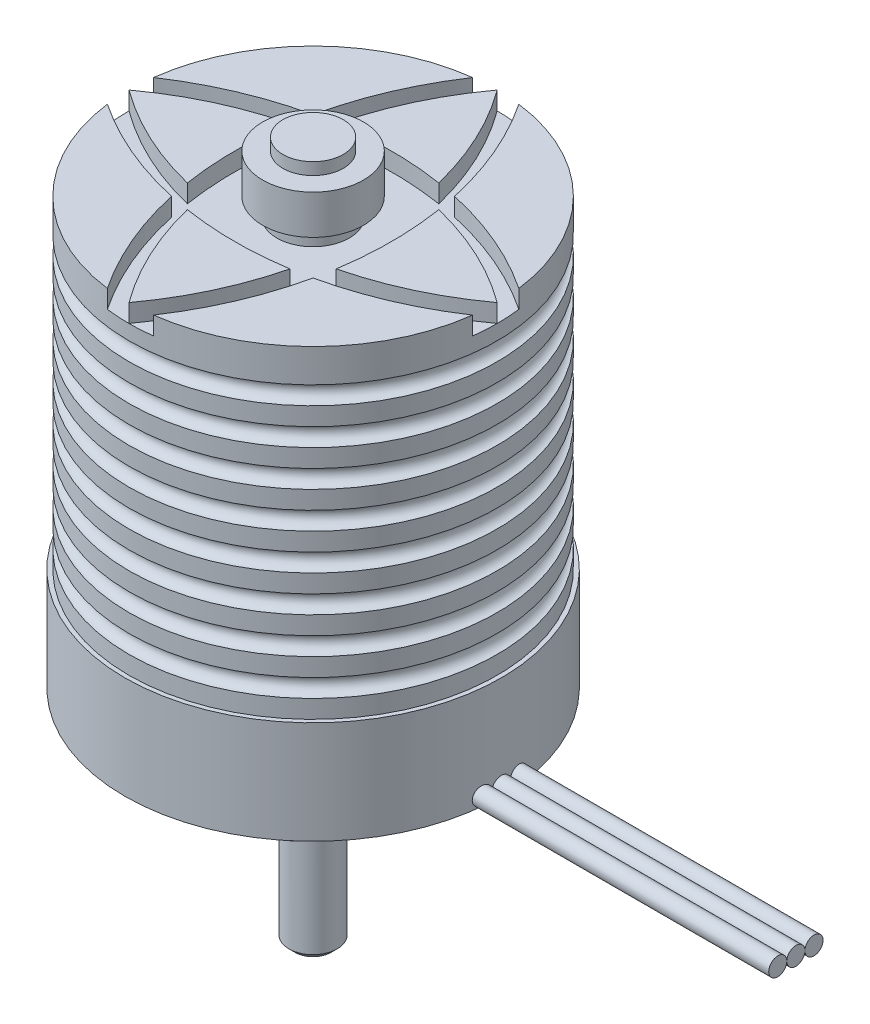
SolidWorks part; units mm, degrees
material "Plain Carbon Steel"
ref_plane "Front" through (0, 0, 0) normal (0, 0, 1) x (1, 0, 0)
ref_plane "Top" through (0, 0, 0) normal (0, 1, 0) x (1, 0, 0)
ref_plane "Right" through (0, 0, 0) normal (1, 0, 0) x (0, 0, -1)
sketch "Sketch1" plane through (0, 0, 0) normal (0, 1, 0) x (1, 0, 0)
  circle A0 centre (0, 0) radius 30.5
  dimension "D1" = 61
extrude "Boss-Extrude1" add sketch "Sketch1" along normal blind 53.5
sketch "Sketch3" plane through (0, 0, 0) normal (0, -1, 0) x (1, 0, 0)
  circle A2 centre (0, 0) radius 31.2
  dimension "D1" = 62.4
ref_plane "Plane1" through (0, -17, 0) normal (0, -1, 0) x (-1, 0, 0)
extrude "Boss-Extrude3" add sketch "Sketch3" along normal up to surface (17 mm away) separate body up to plane "Plane1"
sketch "Sketch2" plane through (0, 0, 0) normal (0, 1, 0) x (1, 0, 0)
  circle A0 centre (0, 0) radius 4
  dimension "D1" = 8
extrude "Boss-Extrude2" add sketch "Sketch2" against normal offset from surface (107 mm away) 36.5 from surface at 53.5 separate body up to face at (0, -17, -31.2) offset beyond the face yes starting at face at (0, 53.5, 30.5)
sketch "Sketch4" plane through (0, 0, 0) normal (0, 0, 1) x (1, 0, 0)
  line L1 (30.5, 0) -> (30.5, 53.5) construction
  line L2 (30.5, 0) -> (-30.5, 0)
  line L3 (30.5, 0) -> (30.5, 53.5)
  line L4 (30.5, 6) -> (30.5, 3)
  line L5 (0, 0) -> (0, 6.4095) construction
  arc A0 (30.5, 6) -> (30.5, 3) centre (30.5, 4.5) ccw
  dimension "D1" = 3
  dimension "D2" = 3
revolve "Cut-Revolve1" cut sketch "Sketch4" angle 360 about L5
pattern_linear "LPattern3" count 8 spacing 6 along (0, 1, 0) of "Cut-Revolve1"
hole_wizard "Tap Drill for M4x0.7 Tap1" positions "Sketch5" profile "Sketch6" hole size "M4x0.7" standard "ANSI Metric" end condition through all
sketch "Sketch5" plane through (0, -17, 0) normal (0, -1, 0) x (-1, 0, 0)
  line L1 (15.5563, 15.5563) -> (-15.5563, 15.5563) construction
  line L2 (15.5563, 15.5563) -> (15.5563, -15.5563) construction
  line L3 (15.5563, -15.5563) -> (-15.5563, -15.5563) construction
  line L4 (-15.5563, 15.5563) -> (-15.5563, -15.5563) construction
  line L5 (15.5563, 15.5563) -> (-15.5563, -15.5563) construction
  line L6 (15.5563, -15.5563) -> (-15.5563, 15.5563) construction
  point P2 (-15.5563, -15.5563)
  point P115 (15.5563, 15.5563)
  point P116 (15.5563, -15.5563)
  point P117 (-15.5563, 15.5563)
  dimension "D1" = 44
sketch "Sketch6" plane through (15.5563, -17, 15.5563) normal (1, 0, 0) x (0, 0, -1)
  line L0 (0, 0) -> (0, 17)
  line L1 (0, 17) -> (1.65, 17)
  line L2 (1.65, 17) -> (1.65, 0)
  line L5 (1.65, 0) -> (0, 0)
  line L11 (0, -6.35) -> (0, 107.95) construction
  dimension "Thru Hole Dia." = 3.3
  dimension "Thru Hole Depth" = 17
pattern_circular "CirPattern1" count 2 every 15 about axis through (0, 0, 0) along (0, 1, 0) of "Tap Drill for M4x0.7 Tap1"
sketch "Sketch7" plane through (0, -53.5, 0) normal (0, -1, 0) x (1, 0, 0)
  circle A1 centre (0, 0) radius 4
  circle A2 centre (0, 0) radius 4
  dimension "D1" = 0
extrude "Cut-Extrude1" cut sketch "Sketch7" against normal through all
sketch "Sketch8" plane through (0, 53.5, 0) normal (0, 1, 0) x (1, 0, 0)
  arc A0 (0, -30.5) -> (0, 30.5) centre (41.5125, 0) cw
  circle A1 centre (0, 0) radius 30.5 construction
  point P8 (-10, 0)
  dimension "D1" = 10
extrude "Cut-Extrude-Thin1" cut sketch "Sketch8" against normal blind 3 and the other way through all thin thin type one direction reverse wall 3
pattern_circular "CirPattern2" count 4 over 360 about axis through (0, 0, 0) along (0, 1, 0) of "Cut-Extrude-Thin1"
sketch "Sketch9" plane through (0, 53.5, 0) normal (0, 1, 0) x (1, 0, 0)
  circle A0 centre (0, 0) radius 6
  arc A4 (9.1761, -9.1761) -> (9.1761, 9.1761) centre (-41.5125, 0) ccw
  arc A5 (9.1761, 9.1761) -> (-9.1761, 9.1761) centre (0, -41.5125) ccw
  arc A6 (-9.1761, 9.1761) -> (-9.1761, -9.1761) centre (41.5125, 0) ccw
  arc A7 (-9.1761, -9.1761) -> (9.1761, -9.1761) centre (0, 41.5125) ccw
  arc A8 (9.1761, -9.1761) -> (9.1761, 9.1761) centre (-41.5125, 0) ccw
  arc A9 (9.1761, 9.1761) -> (-9.1761, 9.1761) centre (0, -41.5125) ccw
  arc A10 (-9.1761, 9.1761) -> (-9.1761, -9.1761) centre (41.5125, 0) ccw
  arc A11 (-9.1761, -9.1761) -> (9.1761, -9.1761) centre (0, 41.5125) ccw
  dimension "D2" = 12
  dimension "D1" = 0
extrude "Cut-Extrude2" cut sketch "Sketch9" against normal up to surface (3 mm away) up to face at (0, 50.5, 0)
ref_plane "Plane2" through (0, 0, 4) normal (0, 0, 1) x (1, 0, 0)
sketch "Sketch10" plane through (0, 0, 4) normal (0, 0, 1) x (1, 0, 0)
  line L0 (0, -30.315) -> (0, -35.485) construction
  line L1 (1.415, -30.315) -> (1.415, -35.485)
  line L2 (-1.415, -30.315) -> (-1.415, -35.485)
  line L4 (-4, -53.5) -> (4, -53.5) construction
  arc A0 (1.415, -30.315) -> (-1.415, -30.315) centre (0, -30.315) ccw
  arc A1 (-1.415, -35.485) -> (1.415, -35.485) centre (0, -35.485) ccw
  point P3 (0, -32.9)
  point P8 (0, -36.9)
  point P9 (0, -28.9)
  dimension "D1" = 2.83
  dimension "D2" = 8
  dimension "D3" = 16.6
extrude "Cut-Extrude3" cut sketch "Sketch10" against normal blind 1.5
sketch "Sketch11" plane through (0, 0, 0) normal (1, 0, 0) x (0, 0, -1)
  line L1 (-31.2, -17) -> (31.2, -17)
  circle A0 centre (-3, -15.5) radius 1.5
  circle A1 centre (0, -15.5) radius 1.5
  circle A2 centre (3, -15.5) radius 1.5
  dimension "D1" = 3
extrude "Boss-Extrude5" add sketch "Sketch11" against normal up to next from offset 80 separate body contours A0 | A1 | A2
sketch "Sketch12" plane through (0, 0, 0) normal (0, 0, 1) x (1, 0, 0)
  line L0 (6, 53.5) -> (-6, 53.5) construction
  line L1 (6, 53.5) -> (-6, 53.5) construction
  line L2 (0, 53.5) -> (0, 62) construction
  line L3 (0, 62) -> (-5, 62)
  line L4 (-5, 62) -> (-5, 60)
  line L5 (-5, 60) -> (-8.35, 60)
  line L6 (-8.35, 60) -> (-8.35, 53.5)
  line L7 (-8.35, 53.5) -> (0, 53.5)
  line L8 (0, 62) -> (0, 53.5)
  dimension "D1" = 16.7
  dimension "D2" = 10
  dimension "D3" = 2
  dimension "D4" = 6.5
revolve "Revolve1" add sketch "Sketch12" angle 360 about L8
ref_plane "Plane3" through (0, 0, 0) normal (0, -1, 0) x (-1, 0, 0)
ref_plane "Plane4" through (0, 53.5, 0) normal (0, 1, 0) x (1, 0, 0)
ref_plane "CanMidplane" through (0, 26.75, 0) normal (0, 1, 0) x (1, 0, 0)
sketch "Sketch13" plane through (0, 26.75, 0) normal (0, 1, 0) x (1, 0, 0)
  circle A0 centre (0, 0) radius 30.5 construction
  circle A1 centre (0, 0) radius 30.5
chamfer "Chamfer1" distance 1 angle 45 1 edges at (0, -53.5, -4)
ref_plane "ShaftMidplane" through (0, -35.25, 0) normal (0, -1, 0) x (-1, 0, 0)
